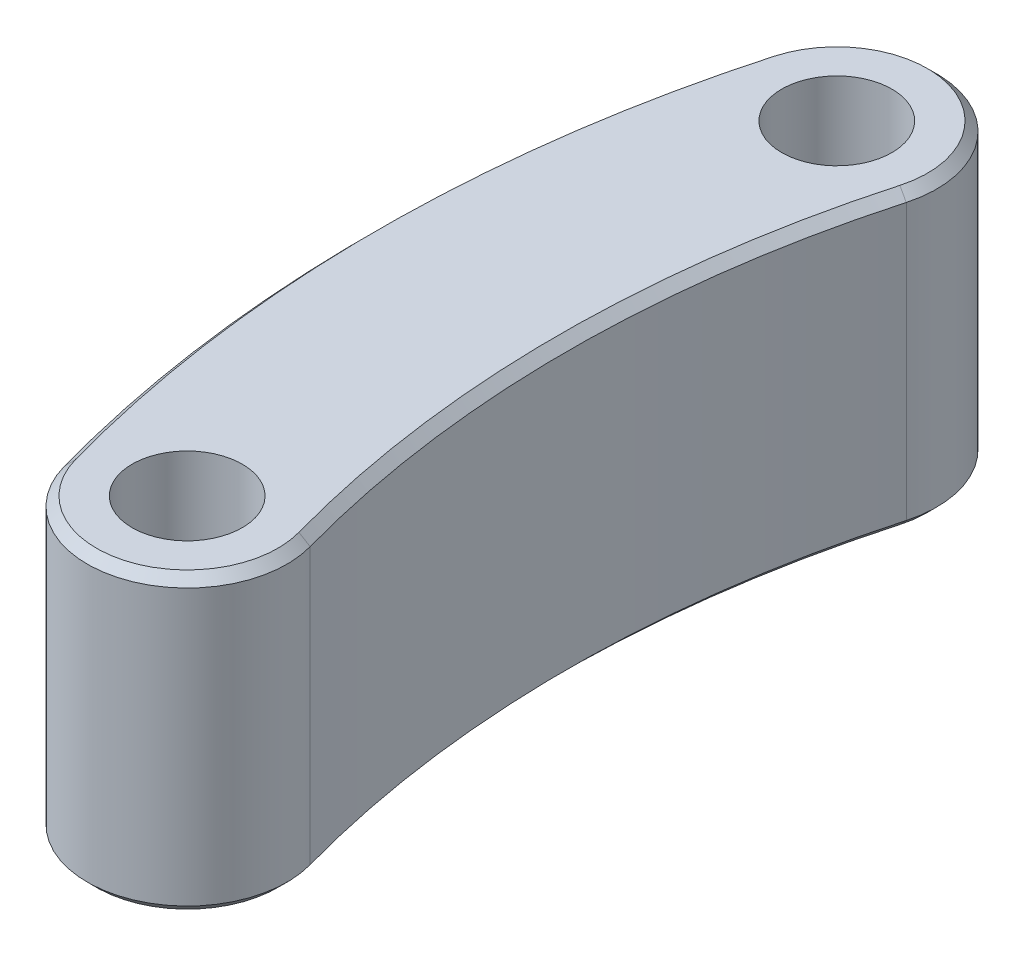
SolidWorks part; units mm, degrees
ref_plane "前视基准面" through (0, 0, 0) normal (0, 0, 1) x (1, 0, 0)
ref_plane "上视基准面" through (0, 0, 0) normal (0, 1, 0) x (1, 0, 0)
ref_plane "右视基准面" through (0, 0, 0) normal (1, 0, 0) x (0, 0, -1)
sketch "草图1" plane through (0, 0, 0) normal (0, 1, 0) x (1, 0, 0)
  line L0 (0, 35.38) -> (0, 0) construction
  circle A0 centre (0, 0) radius 3
  circle A1 centre (0, 35.38) radius 3
  arc A2 (-5.2409, 36.8383) -> (5.2409, 33.9217) centre (0, 35.38) cw
  arc A3 (-5.2409, -1.4583) -> (5.2409, 1.4583) centre (0, 0) ccw
  arc A4 (-5.2409, 36.8383) -> (-5.2409, -1.4583) centre (63.5747, 17.69) ccw
  arc A5 (5.2409, 33.9217) -> (5.2409, 1.4583) centre (63.5747, 17.69) ccw
  dimension "D1" = 6
  dimension "D2" = 35.38
  dimension "D3" = 71.43
  dimension "D4" = 5.44
  dimension "D5" = 60.55
extrude "凸台-拉伸1" add sketch "草图1" along normal blind 16
chamfer "倒角1" distance 0.5 angle 45 8 edges at (3.0247, 0, -17.69) (1.4583, 0, -40.6209) (1.4583, 0, 5.2409) (-7.8553, 0, -17.69) (3.0247, 16, -17.69) (1.4583, 16, -40.6209) (1.4583, 16, 5.2409) (-7.8553, 16, -17.69)
